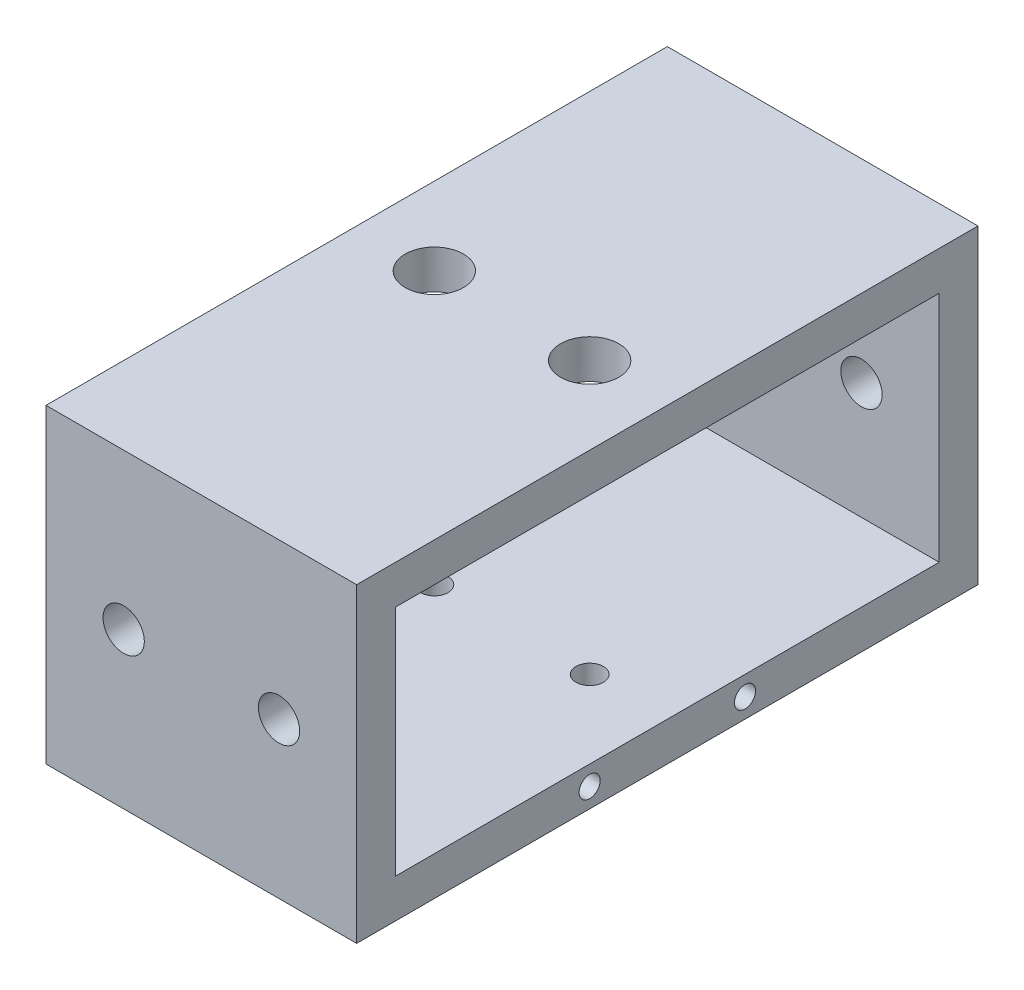
SolidWorks part; units mm, degrees
ref_plane "Front Plane" through (0, 0, 0) normal (0, 0, 1) x (1, 0, 0)
ref_plane "Top Plane" through (0, 0, 0) normal (0, 1, 0) x (1, 0, 0)
ref_plane "Right Plane" through (0, 0, 0) normal (1, 0, 0) x (0, 0, -1)
sketch "Sketch2" plane through (0, 0, 0) normal (1, 0, 0) x (0, 0, -1)
  line L9 (-50.8, -25.4) -> (50.8, -25.4)
  line L10 (-50.8, -25.4) -> (-50.8, 25.4)
  line L11 (-50.8, 25.4) -> (50.8, 25.4)
  line L12 (50.8, -25.4) -> (50.8, 25.4)
  line L13 (-50.8, -25.4) -> (50.8, 25.4) construction
  line L14 (-50.8, 25.4) -> (50.8, -25.4) construction
  line L15 (-44.45, -19.05) -> (44.45, -19.05)
  line L16 (-44.45, -19.05) -> (-44.45, 19.05)
  line L17 (-44.45, 19.05) -> (44.45, 19.05)
  line L18 (44.45, -19.05) -> (44.45, 19.05)
  line L19 (-44.45, -19.05) -> (44.45, 19.05) construction
  line L20 (-44.45, 19.05) -> (44.45, -19.05) construction
  point P0 (0, 0)
  point P5 (0, 0)
  dimension "D1" = 6.35
  dimension "D2" = 101.6
  dimension "D3" = 50.8
  dimension "D4" = 6.35
extrude "Boss-Extrude1" add sketch "Sketch2" along normal mid plane 50.8
sketch "Sketch3" plane through (0, 0, 50.8) normal (0, 0, 1) x (1, 0, 0)
  line L0 (-12.7, 0) -> (12.7, 0)
  point P4 (0, 0)
  dimension "D1" = 25.4
hole_wizard "1/4 Clearance Hole1" positions "Sketch4" profile "Sketch5" hole size "1/4" standard "ANSI Inch" end condition through all
sketch "Sketch4" plane through (0, 0, 50.8) normal (0, 0, 1) x (1, 0, 0)
  point P0 (-12.7, 0)
  point P3 (12.7, 0)
sketch "Sketch5" plane through (-12.7, 0, 50.8) normal (1, 0, 0) x (0, -1, 0)
  line L0 (0, 0) -> (0, 101.6)
  line L1 (0, 101.6) -> (3.3782, 101.6)
  line L2 (3.3782, 101.6) -> (3.3782, 0)
  line L5 (3.3782, 0) -> (0, 0)
  line L11 (0, -6.35) -> (0, 107.95) construction
  dimension "Thru Hole Dia." = 6.7564
  dimension "Thru Hole Depth" = 101.6
sketch "Sketch6" plane through (0, -19.05, 0) normal (0, 1, 0) x (1, 0, 0)
  line L0 (25.4, 0) -> (-25.4, 0) construction
  line L1 (25.4, -44.45) -> (25.4, 44.45) construction
  line L2 (-25.4, -44.45) -> (-25.4, 44.45) construction
  line L3 (6.35, 0) -> (19.05, 0)
  point P9 (12.7, 0)
  point P10 (0, 0)
  dimension "D1" = 12.7
  dimension "D2" = 12.7
hole_wizard "#8 Clearance Hole1" positions "Sketch7" profile "Sketch8" hole size "#8" standard "ANSI Inch"
sketch "Sketch7" plane through (0, -19.05, 0) normal (0, 1, 0) x (1, 0, 0)
  point P0 (12.7, 0)
sketch "Sketch8" plane through (12.7, -19.05, 0) normal (1, 0, 0) x (0, 0, 1)
  line L0 (0, 0) -> (0, 6.35)
  line L1 (0, 6.35) -> (2.2479, 6.35)
  line L2 (2.2479, 6.35) -> (2.2479, 0)
  line L5 (2.2479, 0) -> (0, 0)
  line L11 (0, -6.35) -> (0, 107.95) construction
  dimension "Thru Hole Dia." = 4.4958
  dimension "Thru Hole Depth" = 6.35
mirror "Mirror1" about plane through (0, 0, 0) normal (1, 0, 0) of "#8 Clearance Hole1"
hole_wizard "3/8 (0.375) Diameter Hole1" positions "Sketch10" profile "Sketch11" hole size "3/8" standard "ANSI Inch" end condition up to next
sketch "Sketch10" plane through (0, 25.4, 0) normal (0, 1, 0) x (1, 0, 0)
  circle A0 centre (-12.7, 0) radius 2.2479 construction
  circle A2 centre (12.7, 0) radius 2.2479 construction
  point P0 (-12.7, 0)
  point P3 (12.7, 0)
sketch "Sketch11" plane through (-12.7, 25.4, 0) normal (1, 0, 0) x (0, 0, 1)
  line L0 (0, 0) -> (0, 6.35)
  line L1 (0, 6.35) -> (4.7625, 6.35)
  line L2 (4.7625, 6.35) -> (4.7625, 0)
  line L5 (4.7625, 0) -> (0, 0)
  line L11 (0, -6.35) -> (0, 107.95) construction
  dimension "Thru Hole Dia." = 9.525
  dimension "Thru Hole Depth" = 6.35
hole_wizard "#8-32 Tapped Hole1" positions "Sketch12" profile "Sketch14" tap size "#8-32" standard "ANSI Inch"
sketch "Sketch12" plane through (25.4, 0, 0) normal (-1, 0, 0) x (0, 0, 1)
  line L0 (0, -19.05) -> (0, -25.4) construction
  line L1 (44.45, -19.05) -> (-44.45, -19.05) construction
  line L2 (50.8, -25.4) -> (-50.8, -25.4) construction
  line L4 (-12.7, -22.225) -> (12.7, -22.225) construction
  point P0 (-12.7, -22.225)
  point P2 (12.7, -22.225)
  point P13 (0, -22.225)
  point P18 (0, -22.225)
  dimension "D1" = 25.4
sketch "Sketch14" plane through (25.4, -22.225, -12.7) normal (0, 1, 0) x (0, 0, -1)
  line L0 (0, 0) -> (0, 13.7378)
  line L1 (0, 13.7378) -> (1.7272, 12.7)
  line L2 (1.7272, 12.7) -> (1.7272, 0)
  line L5 (1.7272, 0) -> (0, 0)
  line L10 (0, 13.7378) -> (-1.7272, 12.7) construction
  line L11 (0, -6.35) -> (0, 107.95) construction
  dimension "Tap Drill Dia." = 3.4544
  dimension "Tap Drill Depth" = 12.7
  dimension "Drill Angle" = 118
cosmetic thread "Hole Thread1" parameters "D1"=8.382, "D2"=4.1656
cosmetic thread "Hole Thread2" parameters "D1"=8.382, "D2"=4.1656
equation "\"wall\"=0.25"
equation "\"D1@Sketch2\"=\"wall\""
equation "\"Width\"=4"
equation "\"D2@Sketch2\"=\"Width\""
equation "\"Height\"=2"
equation "\"D3@Sketch2\"=\"Height\""
equation "\"D4@Sketch2\"=\"wall\""
equation "\"Length\"=2"
equation "\"D1@Boss-Extrude1\"=\"Length\""
equation "\"D2@Sketch6\"=\"Length\"/4"
equation "\"D1@Sketch6\"=\"Length\"/4"
